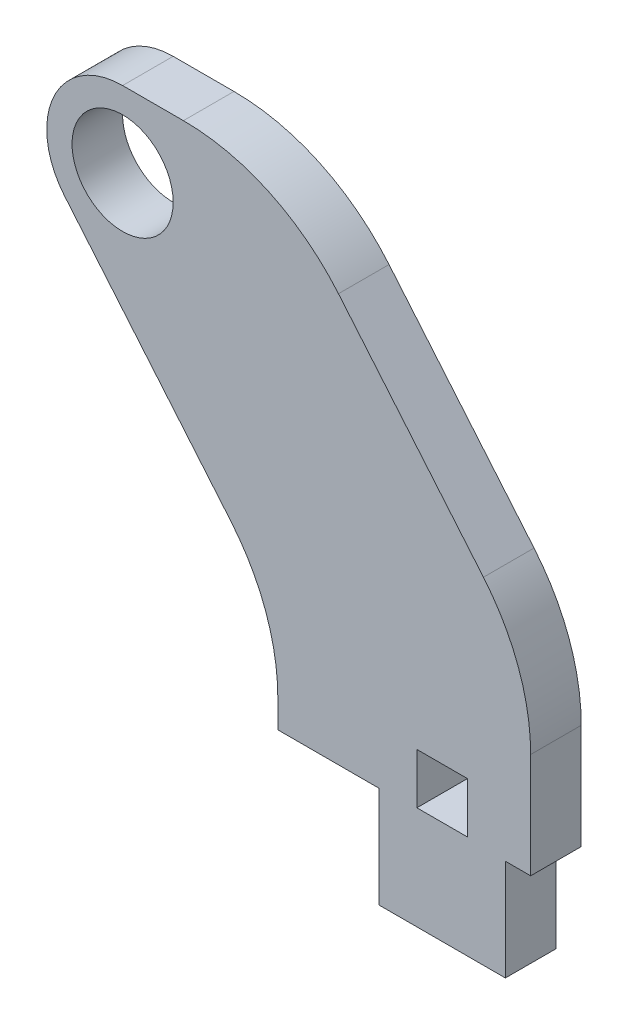
SolidWorks part; units mm, degrees
ref_plane "Front Plane" through (0, 0, 0) normal (0, 0, 1) x (1, 0, 0)
ref_plane "Top Plane" through (0, 0, 0) normal (0, 1, 0) x (1, 0, 0)
ref_plane "Right Plane" through (0, 0, 0) normal (1, 0, 0) x (0, 0, -1)
sketch "Sketch1" plane through (0, 0, 0) normal (0, 0, 1) x (1, 0, 0)
  line L0 (-3.9688, 0) -> (3.9688, 0)
  line L1 (-3.9688, 0) -> (-3.9688, 6.35)
  line L2 (3.9688, 0) -> (3.9688, 6.35)
  line L3 (-3.9688, 6.35) -> (-10.3187, 6.35)
  line L4 (3.9688, 6.35) -> (5.5563, 6.35)
  line L5 (-23.7166, 28.6915) -> (-10.3188, 12.7)
  line L6 (-20.066, 36.5125) -> (-10.3188, 36.5125)
  line L7 (-10.3188, 36.5125) -> (5.5562, 17.5643)
  line L8 (5.5563, 6.35) -> (5.5562, 17.5643)
  line L12 (-10.3188, 12.7) -> (-10.3187, 6.35)
  arc A0 (-20.066, 36.5125) -> (-23.7166, 28.6915) centre (-20.066, 31.75) ccw
  circle A1 centre (-20.066, 31.75) radius 3.175
  dimension "D4" = 6.35
  dimension "D5" = 6.35
  dimension "D10" = 1.5875
  dimension "D1" = 7.9375
  dimension "D2" = 6.35
  dimension "D3" = 1.5875
  dimension "D6" = 6.35
  dimension "D7" = 25.4
  dimension "D8" = 20.066
extrude "Boss-Extrude1" add sketch "Sketch1" along normal blind 3.175
sketch "Sketch2" plane through (0, 0, 3.175) normal (0, 0, 1) x (1, 0, 0)
  line L1 (-1.5875, 9.652) -> (1.5875, 9.652)
  line L2 (-1.5875, 9.652) -> (-1.5875, 6.477)
  line L3 (-1.5875, 6.477) -> (1.5875, 6.477)
  line L4 (1.5875, 9.652) -> (1.5875, 6.477)
  line L5 (-1.5875, 9.652) -> (1.5875, 6.477) construction
  line L6 (-1.5875, 6.477) -> (1.5875, 9.652) construction
  line L7 (-10.3187, 6.35) -> (-3.9688, 6.35) construction
  point P0 (0, 8.0645)
  dimension "D1" = 3.175
  dimension "D2" = 3.175
  dimension "D3" = 0.127
extrude "Cut-Extrude1" cut sketch "Sketch2" against normal up to next
sketch "Sketch6" plane through (0, 0, 3.175) normal (0, 0, 1) x (1, 0, 0)
  line L1 (-6.1186, 17.4625) -> (-14.5189, 17.4625)
  line L3 (-10.3187, 6.35) -> (-3.9688, 6.35) construction
  circle A0 centre (-10.3187, 12.7) radius 4.7625 construction
  arc A1 (-6.1186, 17.4625) -> (-14.5189, 17.4625) centre (-10.3187, 12.7) ccw
  point P0 (-10.3187, 12.7)
  dimension "D1" = 9.525
  dimension "D2" = 12.7
  dimension "D4" = 6.35
extrude "Boss-Extrude2" [suppressed] add sketch "Sketch6" against normal up to surface (3.175 mm away)
hole_wizard "3/8-24 Tapped Hole1" [suppressed] positions "Sketch8" profile "Sketch7" tap size "3/8-24" standard "ANSI Inch"
sketch "Sketch8" plane through (0, 0, 3.175) normal (0, 0, 1) x (1, 0, 0)
  point P0 (-10.3187, 12.7)
sketch "Sketch7" plane through (-10.3187, 12.7, 3.175) normal (1, 0, 0) x (0, -1, 0)
  line L0 (0, 0) -> (0, 26.9175)
  line L1 (0, 26.9175) -> (4.2164, 24.384)
  line L2 (4.2164, 24.384) -> (4.2164, 0)
  line L5 (4.2164, 0) -> (0, 0)
  line L10 (0, 26.9175) -> (-4.2164, 24.384) construction
  line L11 (0, -6.35) -> (0, 107.95) construction
  dimension "Tap Drill Dia." = 8.4328
  dimension "Tap Drill Depth" = 24.384
  dimension "Drill Angle" = 118
sketch "Sketch9" [suppressed] plane through (0, 0, 3.175) normal (0, 0, 1) x (1, 0, 0)
  circle A0 centre (-10.3187, 12.7) radius 2.54
  dimension "D1" = 5.08
extrude "Cut-Extrude2" [suppressed] cut sketch "Sketch9" against normal up to next
fillet "Fillet1" radius 12.7 3 edges at (-10.3188, 12.7, 1.5875) (5.5562, 17.5643, 1.5875) (-10.3188, 36.5125, 1.5875)
